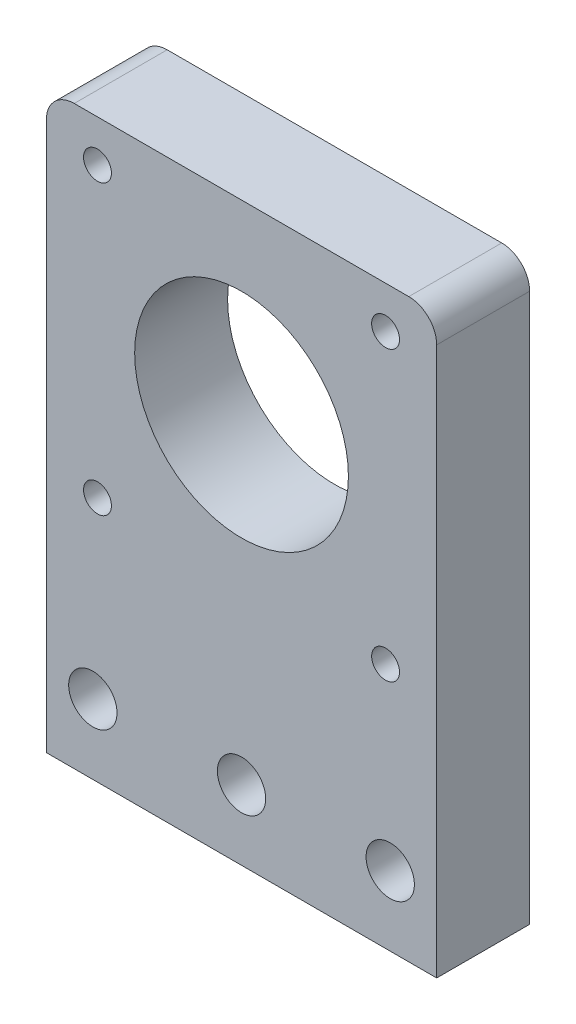
SolidWorks part; units mm, degrees
ref_plane "Front Plane" through (0, 0, 0) normal (0, 0, 1) x (1, 0, 0)
ref_plane "Top Plane" through (0, 0, 0) normal (0, 1, 0) x (1, 0, 0)
ref_plane "Right Plane" through (0, 0, 0) normal (1, 0, 0) x (0, 0, -1)
sketch "Sketch1" plane through (0, 0, 0) normal (0, 0, 1) x (1, 0, 0)
  line L1 (0, 0) -> (42, 0)
  line L2 (0, 0) -> (0, 62)
  line L3 (0, 62) -> (42, 62)
  line L4 (42, 0) -> (42, 62)
  circle A1 centre (21, 42) radius 11.5
  dimension "D3" = 23
  dimension "D1" = 42
  dimension "D2" = 62
  dimension "D4" = 20
extrude "Boss-Extrude1" add sketch "Sketch1" along normal blind 10 contours A1 | L2 L1 L4 L3
fillet "Fillet2" radius 3 2 edges at (42, 62, 5) (0, 62, 5)
sketch "Sketch2" plane through (0, 0, 10) normal (0, 0, 1) x (1, 0, 0)
  line L2 (5.5, 26.5) -> (36.5, 26.5)
  line L3 (5.5, 26.5) -> (5.5, 57.5)
  line L4 (5.5, 57.5) -> (36.5, 57.5)
  line L5 (36.5, 26.5) -> (36.5, 57.5)
  line L6 (5.5, 26.5) -> (36.5, 57.5) construction
  line L7 (5.5, 57.5) -> (36.5, 26.5) construction
  circle A0 centre (5.5, 57.5) radius 1.5
  circle A1 centre (36.5, 57.5) radius 1.5
  circle A2 centre (5.5, 26.5) radius 1.5
  circle A3 centre (36.5, 26.5) radius 1.5
  point P0 (21, 42)
  point P3 (21.8939, 0)
  dimension "D3" = 3
  dimension "D4" = 3
  dimension "D5" = 3
  dimension "D6" = 3
  dimension "D1" = 31
  dimension "D2" = 31
extrude "Cut-Extrude1" cut sketch "Sketch2" against normal through all contours A0 | A1 | A3 | A2
sketch "Sketch3" plane through (0, 0, 10) normal (0, 0, 1) x (1, 0, 0)
  line L0 (0, 0) -> (0, 59) construction
  line L1 (42, 0) -> (42, 59) construction
  line L2 (0, 0) -> (42, 0) construction
  circle A0 centre (5, 7.5) radius 2.6
  circle A1 centre (21, 7.5) radius 2.6
  circle A2 centre (37, 7.5) radius 2.6
  dimension "D1" = 5.2
  dimension "D2" = 5.2
  dimension "D3" = 5.2
  dimension "D6" = 16
  dimension "D5" = 5
  dimension "D4" = 5
  dimension "D7" = 7.5
  dimension "D8" = 7.5
  dimension "D9" = 7.5
extrude "Cut-Extrude2" cut sketch "Sketch3" against normal through all contours A0 | A1 | A2
